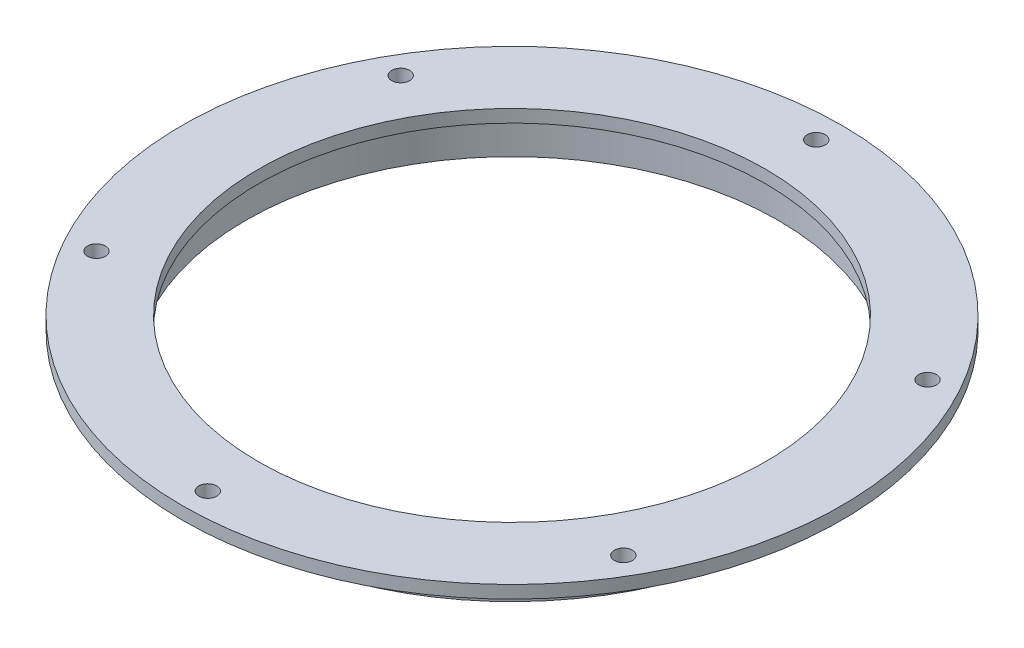
SolidWorks part; units mm, degrees
material "PVC Rigid"
ref_plane "Front Plane" through (0, 0, 0) normal (0, 0, 1) x (1, 0, 0)
ref_plane "Top Plane" through (0, 0, 0) normal (0, 1, 0) x (1, 0, 0)
ref_plane "Right Plane" through (0, 0, 0) normal (1, 0, 0) x (0, 0, -1)
sketch "Sketch1" plane through (0, 0, 0) normal (1, 0, 0) x (0, 0, -1)
  line L0 (66.675, 0) -> (69.85, 0)
  line L1 (69.85, 0) -> (69.85, 9.525)
  line L2 (69.85, 9.525) -> (82.55, 9.525)
  line L3 (82.55, 9.525) -> (82.55, 12.7)
  line L4 (82.55, 12.7) -> (0, 12.7)
  line L5 (0, 12.7) -> (0, 9.525)
  line L6 (0, 9.525) -> (66.675, 9.525)
  line L7 (66.675, 9.525) -> (66.675, 0)
  line L8 (0, 0) -> (0, 12.7) construction
  dimension "D1" = 12.7
  dimension "D2" = 3.175
  dimension "D3" = 69.85
  dimension "D4" = 12.7
  dimension "D5" = 3.175
  dimension "D6" = 12.7
revolve "Revolve1" add sketch "Sketch1" angle 360 about L8
hole_wizard "#8 Clearance Hole1" positions "Sketch2" profile "Sketch3" hole size "#8" standard "ANSI Inch" end condition up to next
sketch "Sketch2" plane through (0, 12.7, 0) normal (0, 1, 0) x (1, 0, 0)
  circle A0 centre (0, 0) radius 82.55 construction
  point P0 (0, 76.2)
  dimension "D1" = 76.2
sketch "Sketch3" plane through (0, 12.7, -76.2) normal (1, 0, 0) x (0, 0, 1)
  line L0 (0, 0) -> (0, 3.176)
  line L1 (0, 3.176) -> (2.2479, 3.176)
  line L2 (2.2479, 3.176) -> (2.2479, 0)
  line L5 (2.2479, 0) -> (0, 0)
  line L11 (0, -6.35) -> (0, 107.95) construction
  dimension "Thru Hole Dia." = 4.4958
  dimension "Thru Hole Depth" = 3.176
pattern_circular "CirPattern1" count 6 over 360 about axis through (0, 0, 0) along (0, 1, 0) of "#8 Clearance Hole1"
sketch "Sketch4" plane through (0, 12.7, 0) normal (0, 1, 0) x (1, 0, 0)
  circle A0 centre (0, 0) radius 63.5
  circle A1 centre (0, 0) radius 82.55 construction
  dimension "D1" = 19.05
extrude "Cut-Extrude1" cut sketch "Sketch4" against normal through all
